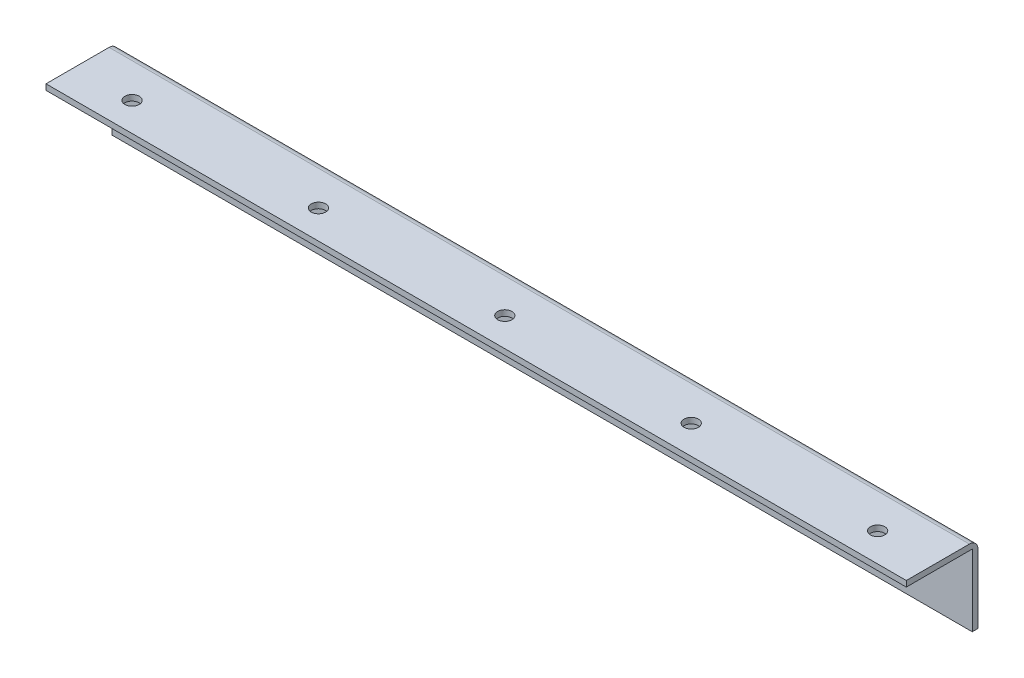
SolidWorks part; units mm, degrees
ref_plane "Plano frontal" through (0, 0, 0) normal (0, 0, 1) x (1, 0, 0)
ref_plane "Plano superior" through (0, 0, 0) normal (0, 1, 0) x (1, 0, 0)
ref_plane "Plano direito" through (0, 0, 0) normal (1, 0, 0) x (0, 0, -1)
sketch "Esboço1" plane through (0, 0, 0) normal (0, 1, 0) x (1, 0, 0)
  line L1 (150, -12.5) -> (-150, -12.5)
  line L2 (150, -12.5) -> (150, 12.5)
  line L3 (150, 12.5) -> (-150, 12.5)
  line L4 (-150, -12.5) -> (-150, 12.5)
  line L5 (150, -12.5) -> (-150, 12.5) construction
  line L6 (150, 12.5) -> (-150, -12.5) construction
  point P0 (0, 0)
  dimension "D1" = 25
  dimension "D2" = 300
extrude "Ressalto-extrusão1" add sketch "Esboço1" along normal blind 2
sketch "Esboço2" plane through (0, 2, 0) normal (0, 1, 0) x (1, 0, 0)
  line L0 (-170.4364, -2.5) -> (181.9659, -2.5) construction
  line L1 (-150, -12.5) -> (150, -12.5) construction
  line L2 (0, 25.2941) -> (0, -29.6609) construction
  line L3 (-150, 12.5) -> (-150, -12.5) construction
  circle A0 centre (-130, -2.5) radius 2.5
  circle A1 centre (-65, -2.5) radius 2.5
  circle A2 centre (0, -2.5) radius 2.5
  circle A3 centre (65, -2.5) radius 2.5
  circle A4 centre (130, -2.5) radius 2.5
  dimension "D2" = 5
  dimension "D3" = 20
  dimension "D4" = 65
  dimension "D1" = 10
extrude "Corte-extrusão1" cut sketch "Esboço2" against normal through all
sketch "Esboço3" plane through (0, 0, 0) normal (0, -1, 0) x (1, 0, 0)
  line L0 (150, 12.5) -> (150, -12.5) construction
  line L1 (-150, -12.5) -> (150, -12.5)
  line L2 (-150, -12.5) -> (-150, -10.5)
  line L3 (-150, -10.5) -> (150, -10.5)
  line L4 (150, -12.5) -> (150, -10.5)
  dimension "D1" = 2
extrude "Ressalto-extrusão2" add sketch "Esboço3" along normal blind 25
fillet "Filete1" radius 3 1 edges at (0, 2, -12.5)
